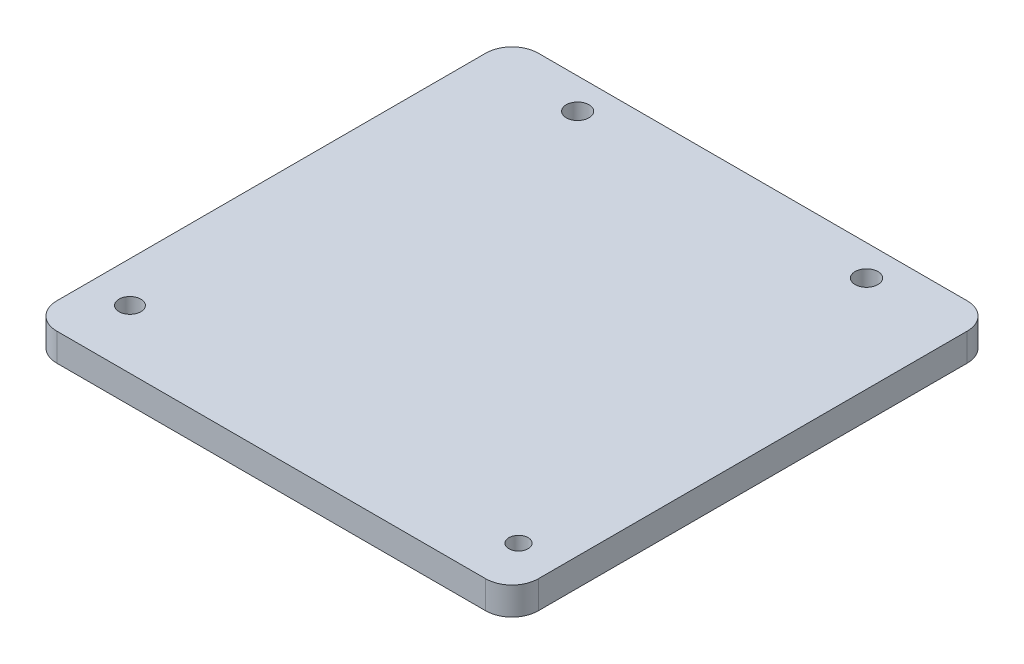
SolidWorks part; units mm, degrees
ref_plane "Front Plane" through (0, 0, 0) normal (0, 0, 1) x (1, 0, 0)
ref_plane "Top Plane" through (0, 0, 0) normal (0, 1, 0) x (1, 0, 0)
ref_plane "Right Plane" through (0, 0, 0) normal (1, 0, 0) x (0, 0, -1)
sketch "Sketch1" plane through (0, 0, 0) normal (0, 1, 0) x (1, 0, 0)
  line L1 (-27.5, 27.5) -> (27.5, 27.5)
  line L2 (-27.5, 27.5) -> (-27.5, -27.5)
  line L3 (-27.5, -27.5) -> (27.5, -27.5)
  line L4 (27.5, 27.5) -> (27.5, -27.5)
  line L5 (-27.5, 27.5) -> (27.5, -27.5) construction
  line L6 (-27.5, -27.5) -> (27.5, 27.5) construction
  point P0 (0, 0)
  dimension "D1" = 55
  dimension "D2" = 55
extrude "Boss-Extrude1" add sketch "Sketch1" along normal blind 3.175
fillet "Fillet1" radius 3 4 edges at (-27.5, 1.5875, 27.5) (27.5, 1.5875, 27.5) (27.5, 1.5875, -27.5) (-27.5, 1.5875, -27.5)
sketch "Sketch3" plane through (0, 3.175, 0) normal (0, 1, 0) x (1, 0, 0)
  line L0 (-27.5, 0) -> (27.5, 0) construction
  line L1 (-22.865, -3) -> (22.855, -3) construction
  line L2 (-22.865, -3) -> (-22.865, -20.78) construction
  line L3 (-22.865, -20.78) -> (22.855, -22.11) construction
  line L4 (22.855, -3) -> (22.855, -22.11) construction
  line L5 (-27.5, 24.5) -> (-27.5, -24.5) construction
  line L6 (27.5, -24.5) -> (27.5, 24.5) construction
  circle A2 centre (22.855, -22.11) radius 1.1
  circle A3 centre (-22.865, -20.78) radius 1.25
  dimension "D2" = 45.72
  dimension "D3" = 17.78
  dimension "D4" = 19.11
  dimension "D5" = 45.72
  dimension "D7" = 3
extrude "Cut-Extrude2" cut sketch "Sketch3" against normal up to surface (3.175 mm away) up to face at (0, 0, 0)
sketch "Sketch6" plane through (0, 3.175, 0) normal (0, 1, 0) x (1, 0, 0)
  line L0 (0, 27.5) -> (0, -27.5) construction
  line L1 (24.5, 27.5) -> (-24.5, 27.5) construction
  line L2 (-24.5, -27.5) -> (24.5, -27.5) construction
  circle A0 centre (-16.5, 24) radius 1.3
  circle A1 centre (16.5, 24) radius 1.3
  dimension "D1" = 2.6
  dimension "D2" = 16.5
  dimension "D3" = 3.5
extrude "Cut-Extrude5" cut sketch "Sketch6" against normal up to surface (3.175 mm away) up to face at (22.855, 0, 23.21)
